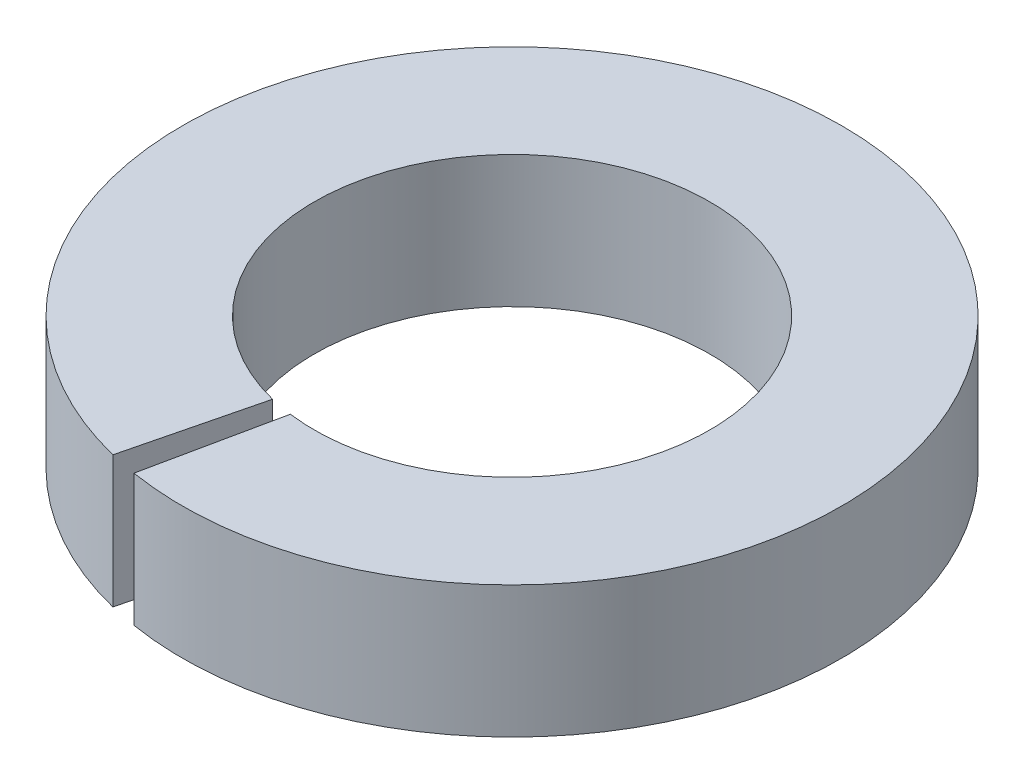
SolidWorks part; units mm, degrees
ref_plane "Спереди" through (0, 0, 0) normal (0, 0, 1) x (1, 0, 0)
ref_plane "Сверху" through (0, 0, 0) normal (0, 1, 0) x (1, 0, 0)
ref_plane "Справа" through (0, 0, 0) normal (1, 0, 0) x (0, 0, -1)
sketch "Эскиз1" plane through (0, 0, 0) normal (0, 1, 0) x (1, 0, 0)
  line L0 (-0.3607, -1.456) -> (-0.6012, -2.4266)
  line L1 (-0.4008, -2.4677) -> (-0.1948, -1.4873)
  arc A0 (-0.1948, -1.4873) -> (-0.3607, -1.456) centre (0, 0) ccw
  arc A1 (-0.4008, -2.4677) -> (-0.6012, -2.4266) centre (0, 0) ccw
  dimension "D1" = 5
  dimension "D2" = 3
extrude "Бобышка-Вытянуть1" add sketch "Эскиз1" along normal blind 1
